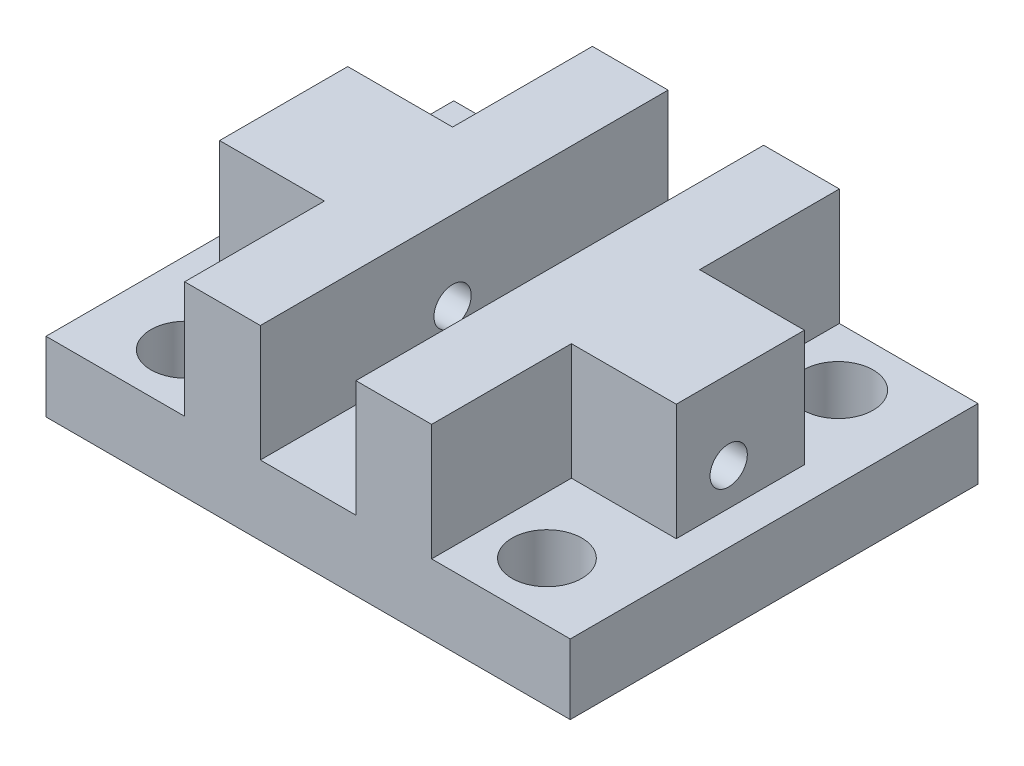
SolidWorks part; units mm, degrees
ref_plane "Plan de face" through (0, 0, 0) normal (0, 0, 1) x (1, 0, 0)
ref_plane "Plan de dessus" through (0, 0, 0) normal (0, 1, 0) x (1, 0, 0)
ref_plane "Plan de droite" through (0, 0, 0) normal (1, 0, 0) x (0, 0, -1)
sketch "Esquisse1" plane through (0, 0, 0) normal (0, 1, 0) x (1, 0, 0)
  line L1 (-22.5, 18.5) -> (22.5, 18.5)
  line L2 (-22.5, 18.5) -> (-22.5, -16.5)
  line L3 (-22.5, -16.5) -> (22.5, -16.5)
  line L4 (22.5, 18.5) -> (22.5, -16.5)
  dimension "D1" = 45
  dimension "D2" = 35
  dimension "D3" = 22.5
  dimension "D4" = 16.5
extrude "Boss.-Extru.1" add sketch "Esquisse1" along normal blind 6
sketch "Esquisse2" plane through (0, 6, 0) normal (0, 1, 0) x (1, 0, 0)
  line L0 (22.5, -16.5) -> (22.5, 18.5) construction
  line L2 (22.5, 18.5) -> (-22.5, 18.5) construction
  line L3 (-22.5, -16.5) -> (22.5, -16.5) construction
  line L4 (-22.5, 18.5) -> (-22.5, -16.5) construction
  circle A0 centre (-15.5, 13.5) radius 3
  circle A1 centre (-15.5, -11.5) radius 3
  circle A2 centre (15.5, -11.5) radius 3
  circle A3 centre (15.5, 13.5) radius 3
  dimension "D1" = 6
  dimension "D2" = 6
  dimension "D3" = 6
  dimension "D4" = 6
  dimension "D9" = 5
  dimension "D10" = 5
  dimension "D5" = 25
  dimension "D6" = 25
  dimension "D7" = 31
  dimension "D8" = 7
  dimension "D11" = 7
extrude "Enlèv. mat.-Extru.1" cut sketch "Esquisse2" against normal through all
sketch "Esquisse3" plane through (0, 6, 0) normal (0, 1, 0) x (1, 0, 0)
  line L1 (-4.1, 8.1) -> (4.1, 8.1)
  line L2 (-4.1, 8.1) -> (-4.1, -8.1)
  line L3 (-4.1, -8.1) -> (4.1, -8.1)
  line L4 (4.1, 8.1) -> (4.1, -8.1)
  dimension "D1" = 16.2
  dimension "D2" = 8.2
  dimension "D3" = 4.1
  dimension "D4" = 8.1
extrude "Enlèv. mat.-Extru.2" cut sketch "Esquisse3" against normal through all
sketch "Esquisse4" plane through (-4.1, 0, 0) normal (1, 0, 0) x (0, 0, -1)
  line L1 (-16.5, 6) -> (18.5, 6)
  line L2 (-16.5, 6) -> (-16.5, 16)
  line L3 (-16.5, 16) -> (18.5, 16)
  line L4 (18.5, 6) -> (18.5, 16)
  dimension "D1" = 10
extrude "Boss.-Extru.2" add sketch "Esquisse4" against normal blind 6.5 contours L3 L4 L1 L2
sketch "Esquisse5" plane through (4.1, 0, -4) normal (-1, 0, 0) x (0, 0, 1)
  line L1 (-14.5, 6) -> (20.5, 6)
  line L2 (-14.5, 6) -> (-14.5, 16)
  line L3 (-14.5, 16) -> (20.5, 16)
  line L4 (20.5, 6) -> (20.5, 16)
  dimension "D1" = 10
extrude "Boss.-Extru.3" add sketch "Esquisse5" against normal blind 6.5 contours L3 L4 L1 L2
sketch "Esquisse7" plane through (10.6, 0, 0) normal (1, 0, 0) x (0, 0, -1)
  line L0 (18.5, 16) -> (-16.5, 16) construction
  line L1 (-4.5, 16) -> (6.5, 16)
  line L2 (-4.5, 16) -> (-4.5, 6)
  line L3 (-4.5, 6) -> (6.5, 6)
  line L4 (6.5, 16) -> (6.5, 6)
  line L5 (18.5, 6) -> (-16.5, 6) construction
  dimension "D1" = 12
  dimension "D2" = 12
extrude "Boss.-Extru.4" add sketch "Esquisse7" along normal blind 9
sketch "Esquisse8" plane through (-10.6, 0, -10.5) normal (1, 0, 0) x (0, 0, -1)
  line L1 (-15, 16) -> (-4, 16)
  line L2 (-15, 16) -> (-15, 6)
  line L3 (-15, 6) -> (-4, 6)
  line L4 (-4, 16) -> (-4, 6)
  line L6 (8, 6) -> (8, 16) construction
  line L7 (-27, 16) -> (8, 16) construction
  dimension "D1" = 12
  dimension "D2" = 12
extrude "Boss.-Extru.5" add sketch "Esquisse8" against normal blind 9 contours L2 L3 L4 L1
sketch "Esquisse6" plane through (10.6, 0, 0) normal (1, 0, 0) x (0, 0, -1)
  line L1 (18.5, 6) -> (18.5, 16) construction
  line L4 (-4.5, 6) -> (6.5, 6) construction
  circle A0 centre (0, 9.2) radius 1.6
  dimension "D1" = 3.2
  dimension "D2" = 3.2
  dimension "D3" = 18.5
extrude "Enlèv. mat.-Extru.3" cut sketch "Esquisse6" against normal through all and the other way through all
